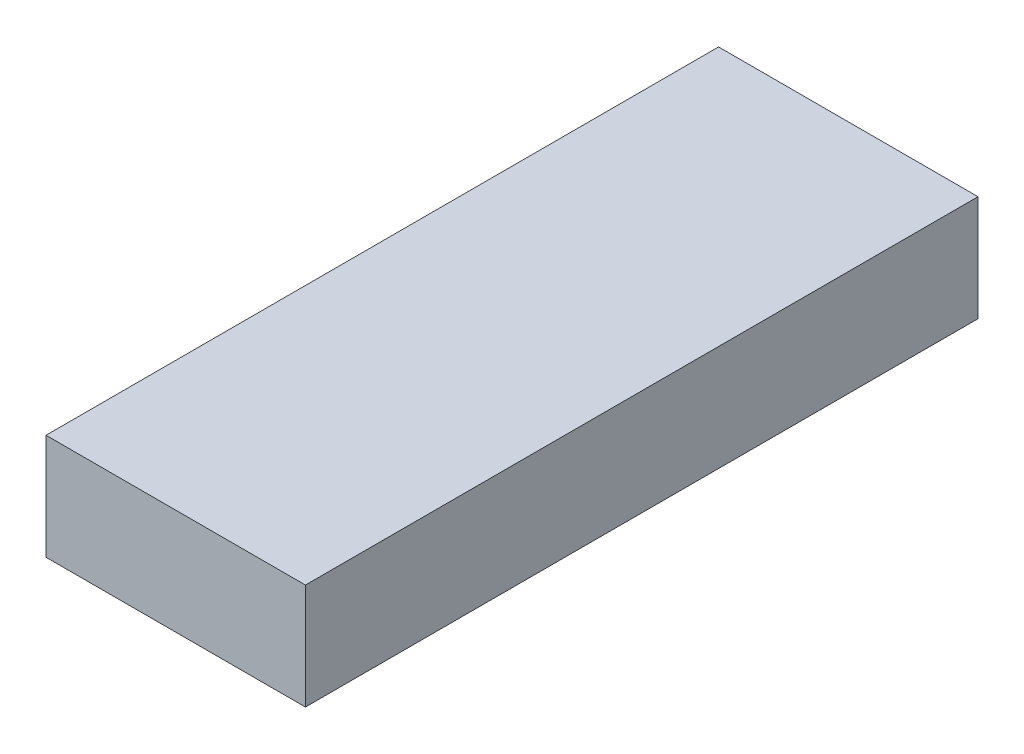
SolidWorks part; units mm, degrees
ref_plane "Front Plane" through (0, 0, 0) normal (0, 0, 1) x (1, 0, 0)
ref_plane "Top Plane" through (0, 0, 0) normal (0, 1, 0) x (1, 0, 0)
ref_plane "Right Plane" through (0, 0, 0) normal (1, 0, 0) x (0, 0, -1)
sketch "Sketch1" plane through (0, 0, 0) normal (0, 1, 0) x (1, 0, 0)
  line L0 (0, 35) -> (0, -35) construction
  line L1 (-13.5, 35) -> (13.5, 35)
  line L2 (-13.5, 35) -> (-13.5, -35)
  line L3 (-13.5, -35) -> (13.5, -35)
  line L4 (13.5, 35) -> (13.5, -35)
  line L5 (-13.5, 0) -> (13.5, 0) construction
  point P8 (0, 0)
  dimension "D1" = 27
  dimension "D2" = 70
extrude "Boss-Extrude1" add sketch "Sketch1" along normal blind 11
